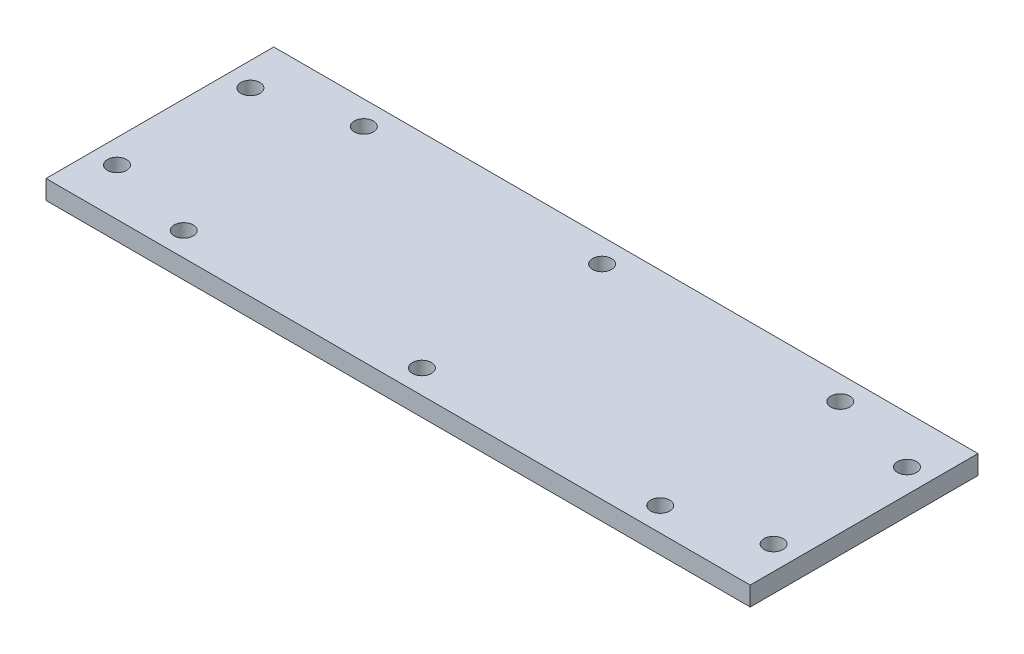
SolidWorks part; units mm, degrees
material "ABS PC"
ref_plane "Front Plane" through (0, 0, 0) normal (0, 0, 1) x (1, 0, 0)
ref_plane "Top Plane" through (0, 0, 0) normal (0, 1, 0) x (1, 0, 0)
ref_plane "Right Plane" through (0, 0, 0) normal (1, 0, 0) x (0, 0, -1)
sketch "Sketch1" plane through (0, 0, 0) normal (0, 1, 0) x (1, 0, 0)
  line L0 (0, 0) -> (-12.8519, 0) construction
  line L1 (-36.95, -11.95) -> (36.95, -11.95)
  line L2 (-36.95, -11.95) -> (-36.95, 11.95)
  line L3 (-36.95, 11.95) -> (36.95, 11.95)
  line L4 (36.95, -11.95) -> (36.95, 11.95)
  line L5 (-36.95, -11.95) -> (36.95, 11.95) construction
  line L6 (-36.95, 11.95) -> (36.95, -11.95) construction
  line L7 (0, 0) -> (0, 4.7059) construction
  circle A0 centre (-25, 9.45) radius 1
  circle A1 centre (0, 9.45) radius 1
  circle A2 centre (25, 9.45) radius 1
  circle A3 centre (-34.45, 7) radius 1
  circle A4 centre (25, -9.45) radius 1
  circle A5 centre (0, -9.45) radius 1
  circle A6 centre (-25, -9.45) radius 1
  circle A7 centre (-34.45, -7) radius 1
  circle A8 centre (34.45, -7) radius 1
  circle A9 centre (34.45, 7) radius 1
  point P0 (0, 0)
  dimension "D3" = 2
  dimension "D4" = 25
  dimension "D5" = 25
  dimension "D6" = 2.5
  dimension "D7" = 2.5
  dimension "D8" = 7
  dimension "D9" = 2
  dimension "D1" = 23.9
  dimension "D2" = 73.9
extrude "Boss-Extrude1" add sketch "Sketch1" along normal blind 2
